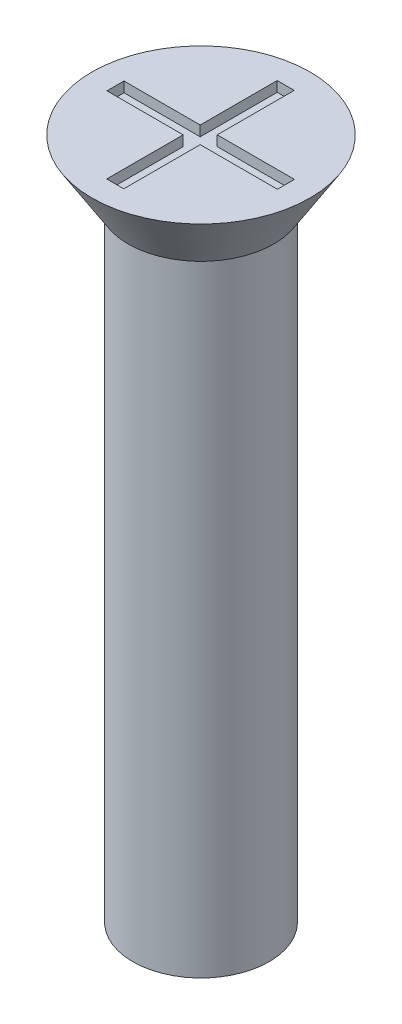
SolidWorks part; units mm, degrees
material "AISI 304"
ref_plane "Front" through (0, 0, 0) normal (0, 0, 1) x (1, 0, 0)
ref_plane "Top" through (0, 0, 0) normal (0, 1, 0) x (1, 0, 0)
ref_plane "Right" through (0, 0, 0) normal (1, 0, 0) x (0, 0, -1)
sketch "Sketch1" plane through (0, 0, 0) normal (0, 1, 0) x (1, 0, 0)
  circle A0 centre (0, 0) radius 2
  dimension "D1" = 4
extrude "Boss-Extrude1" add sketch "Sketch1" along normal blind 20
sketch "Sketch2" plane through (0, 20, 0) normal (0, 1, 0) x (1, 0, 0)
  circle A0 centre (0, 0) radius 3.2
  dimension "D1" = 6.4
extrude "Boss-Extrude2" add sketch "Sketch2" against normal blind 1.7 draft 32
sketch "Sketch3" plane through (0, 20, 0) normal (0, 1, 0) x (1, 0, 0)
  line L1 (-2.5, 0.2416) -> (2.5, 0.2416)
  line L2 (-2.5, 0.2416) -> (-2.5, -0.2584)
  line L3 (-2.5, -0.2584) -> (2.5, -0.2584)
  line L4 (2.5, 0.2416) -> (2.5, -0.2584)
  line L5 (-0.2653, 2.5) -> (0.2347, 2.5)
  line L6 (-0.2653, 2.5) -> (-0.2653, -2.5)
  line L7 (-0.2653, -2.5) -> (0.2347, -2.5)
  line L8 (0.2347, 2.5) -> (0.2347, -2.5)
  circle A0 centre (0, 0) radius 3.2 construction
  dimension "D1" = 0.5
  dimension "D2" = 0.5
  dimension "D3" = 5
  dimension "D4" = 5
  dimension "D5" = 2.5
  dimension "D6" = 2.5
extrude "Cut-Extrude1" cut sketch "Sketch3" against normal blind 0.3 contours L8 L5 L6 L1 | L8 L3 L6 L7 | L6 L1 L2 L3 | L1 L8 L3 L4 | L8 L1 L6 L3
